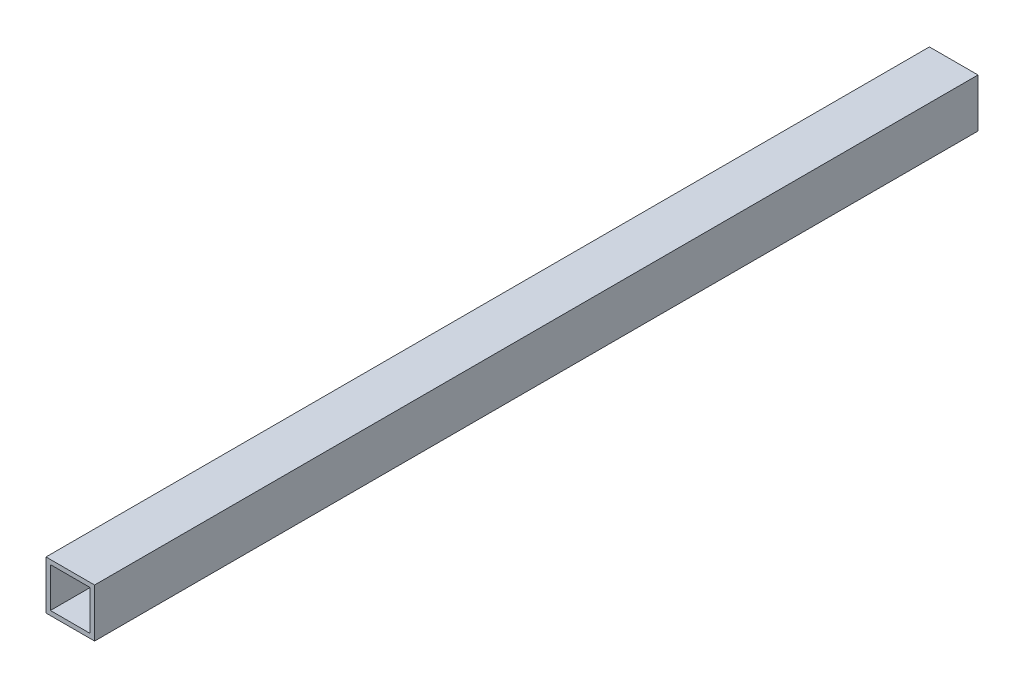
SolidWorks part; units mm, degrees
ref_plane "Front Plane" through (0, 0, 0) normal (0, 0, 1) x (1, 0, 0)
ref_plane "Top Plane" through (0, 0, 0) normal (0, 1, 0) x (1, 0, 0)
ref_plane "Right Plane" through (0, 0, 0) normal (1, 0, 0) x (0, 0, -1)
sketch "Sketch2" plane through (0, 0, 0) normal (0, 0, 1) x (1, 0, 0)
  line L1 (-38.7059, 39.0294) -> (1.2941, 39.0294)
  line L2 (-38.7059, 39.0294) -> (-38.7059, -0.9706)
  line L3 (-38.7059, -0.9706) -> (1.2941, -0.9706)
  line L4 (1.2941, 39.0294) -> (1.2941, -0.9706)
  line L5 (-38.7059, 39.0294) -> (1.2941, -0.9706) construction
  line L6 (-38.7059, -0.9706) -> (1.2941, 39.0294) construction
  point P0 (-18.7059, 19.0294)
  dimension "D1" = 40
  dimension "D2" = 40
extrude "Extrude-Thin1" add sketch "Sketch2" along normal mid plane 800 thin thin type mid plane wall 4
